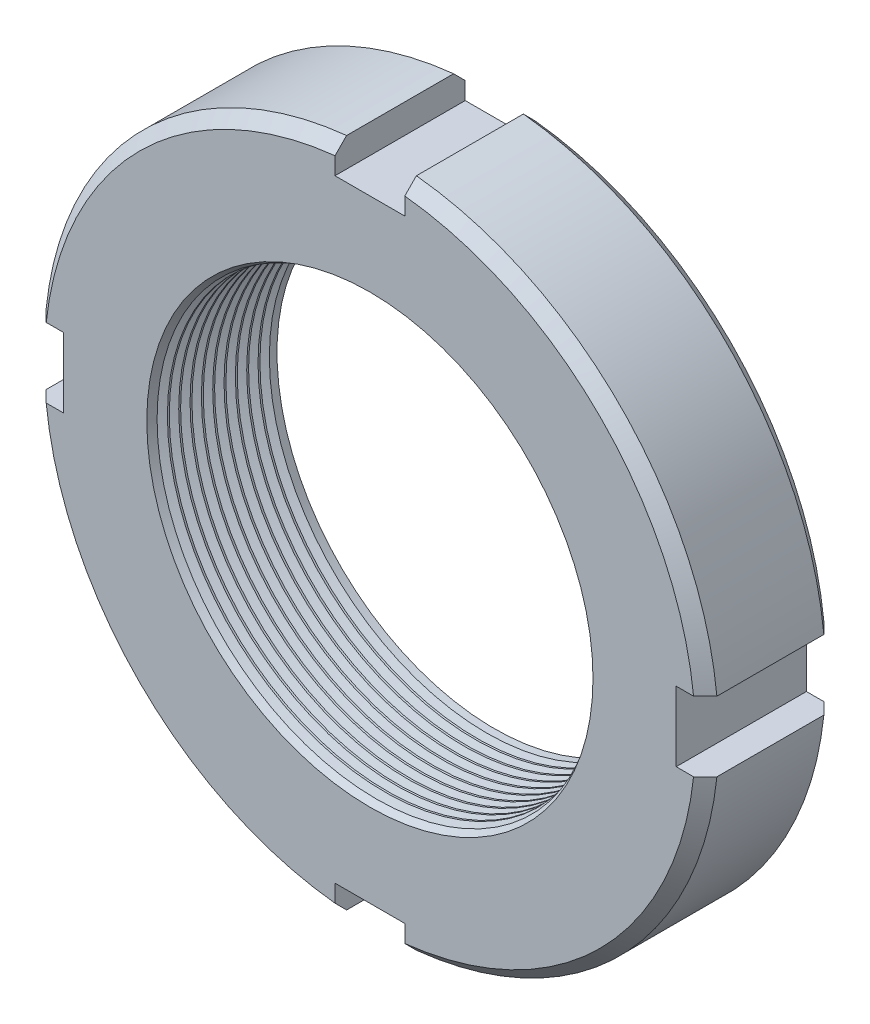
SolidWorks part; units mm, degrees
ref_plane "Front" through (0, 0, 0) normal (0, 0, 1) x (1, 0, 0)
ref_plane "Top" through (0, 0, 0) normal (0, 1, 0) x (1, 0, 0)
ref_plane "Right" through (0, 0, 0) normal (1, 0, 0) x (0, 0, -1)
sketch "Sketch2" plane through (0, 0, 0) normal (0, 0, 1) x (1, 0, 0)
  circle A0 centre (0, 0) radius 29
  dimension "dk" = 58
extrude "BaseNut" add sketch "Sketch2" against normal blind 11.2
chamfer "Chamfer1" distance 1 angle 45 2 edges at (29, 0, -11.2) (29, 0, 0)
sketch "Sketch3" plane through (-17.5617, 31.6827, 0) normal (0, 0, 1) x (1, 0, 0)
  circle A0 centre (17.5617, -31.6827) radius 18.688
  circle A1 centre (17.5617, -31.6827) radius 28 construction
  dimension "D1" = 37.376
extrude "Hole" cut sketch "Sketch3" against normal through all
cosmetic thread "ThreadCosmetic1" [suppressed] parameters "D2"=39
chamfer "EndChamfer" distance 0.5 angle 60 2 edges at (18.688, 0, 0) (18.688, 0, -11.2)
sketch "Sketch4" plane through (-28.8484, 49.2663, 0) normal (0, 0, 1) x (1, 0, 0)
  line L0 (28.8484, 68.6571) -> (28.8484, -68.9081) construction
  line L2 (25.8484, -20.4219) -> (31.8484, -20.4219) construction
  line L3 (25.8484, -20.4219) -> (25.8484, -22.9219)
  line L4 (25.8484, -22.9219) -> (31.8484, -22.9219)
  line L5 (31.8484, -20.4219) -> (31.8484, -22.9219)
  arc A1 (31.8484, -20.4219) -> (25.8484, -20.4219) centre (28.8484, -49.2663) ccw
  circle A2 centre (28.8484, -49.2663) radius 29 construction
  dimension "n" = 6
  dimension "t" = 2.5
extrude "SlotCut" cut sketch "Sketch4" against normal through all
pattern_circular "SlotPat" count 4 over 360 about axis through (0, 0, 0) along (0, 0, 1) of "SlotCut"
sketch "Sketch5" plane through (0, 0, 0) normal (0, 1, 0) x (1, 0, 0)
  line L0 (17.876, 1.272) -> (17.876, 0.46)
  line L1 (17.876, 0.46) -> (18.688, 0.46)
  line L2 (18.688, 0.46) -> (19.3912, 0.866)
  line L3 (19.3912, 0.866) -> (18.688, 1.272)
  line L4 (18.688, 1.272) -> (17.876, 1.272)
  line L5 (0, 37.3018) -> (0, -33.5096) construction
  line L9 (18.688, 0.866) -> (-18.688, 0.866) construction
  dimension "D1" = 0.812
  dimension "D2" = 37.376
revolve "Cut-Revolve10" cut sketch "Sketch5" angle 360 about L5
pattern_linear "LPattern10" count 10 spacing 0.9744 along (0, 0, -1) of "Cut-Revolve10"
equation "\"D1@Sketch5\" =  ( \"D2@ThreadCosmetic1\" - \"D1@Sketch3\" )  / 2"
equation "\"D3@LPattern10\" = \"D1@Sketch5\" * 1.2"
equation "\"D1@LPattern10\" = \"m@BaseNut\" / \"D3@LPattern10\"-1"
equation "\"D2@Sketch5\" = \"D1@Sketch3\""
